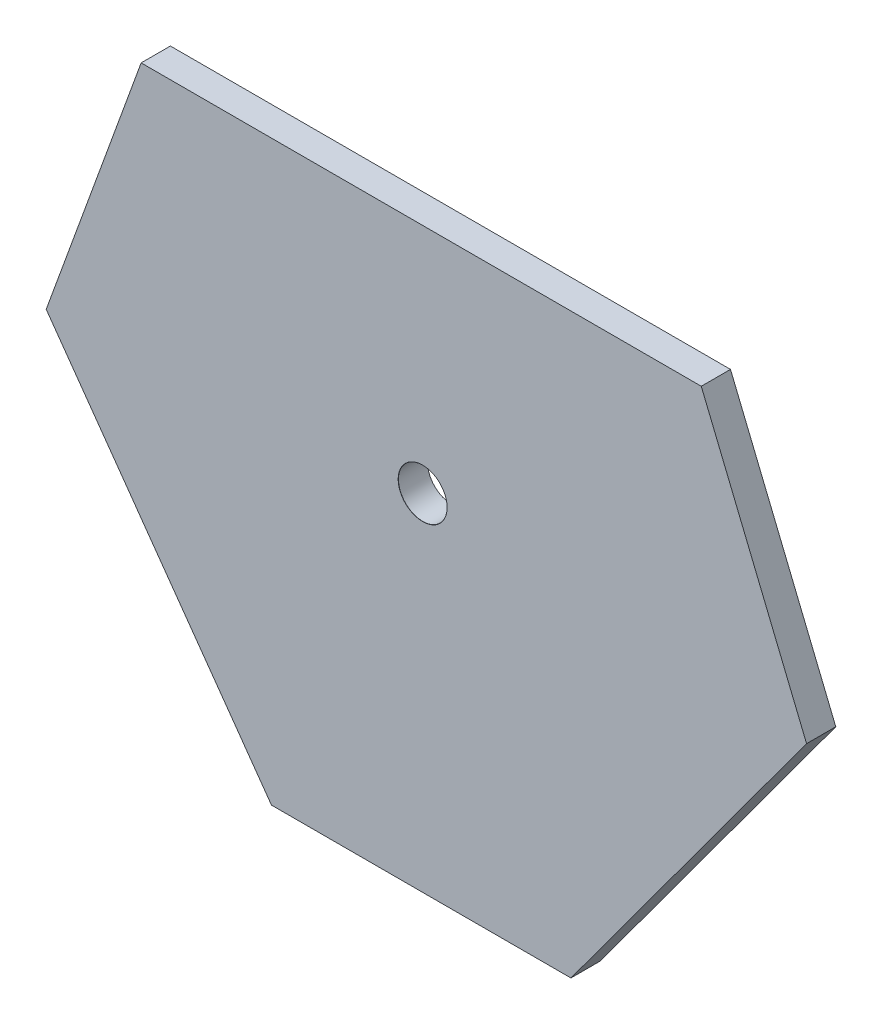
SolidWorks part; units mm, degrees
ref_plane "Front Plane" through (0, 0, 0) normal (0, 0, 1) x (1, 0, 0)
ref_plane "Top Plane" through (0, 0, 0) normal (0, 1, 0) x (1, 0, 0)
ref_plane "Right Plane" through (0, 0, 0) normal (1, 0, 0) x (0, 0, -1)
sketch "Sketch1" plane through (0, 0, 0) normal (0, 0, 1) x (1, 0, 0)
  line L0 (-47.9271, -8.0808) -> (13.5529, -8.0808) construction
  line L1 (-47.9271, -8.0808) -> (13.5529, -8.0808)
  line L3 (-74.6871, 110.5195) -> (40.3129, 110.5195)
  line L4 (-74.6871, 110.5195) -> (-94.1823, 56.957)
  line L5 (40.3129, 110.5195) -> (61.9322, 57.7786)
  line L6 (-94.1823, 56.957) -> (-47.9271, -8.0808)
  line L7 (13.5529, -8.0808) -> (61.9322, 57.7786)
  point P2 (0, 0)
  point P9 (-17.1871, 110.5195)
extrude "Boss-Extrude1" add sketch "Sketch1" along normal blind 6
hole_wizard "Ø10.0mm Dowel Hole2" positions "Sketch4" profile "Sketch5" hole size "Ø10.0" standard "GB"
sketch "Sketch4" plane through (0, 0, 6) normal (0, 0, 1) x (1, 0, 0)
  point P0 (-16.8906, 62.8731)
sketch "Sketch5" plane through (-16.8906, 62.8731, 6) normal (1, 0, 0) x (0, -1, 0)
  line L0 (0, 0) -> (0, 53.0043)
  line L1 (0, 53.0043) -> (5, 50)
  line L2 (5, 50) -> (5, 0.025)
  line L3 (5, 0.025) -> (5.025, 0)
  line L5 (5.025, 0) -> (0, 0)
  line L6 (-5, 0.025) -> (-5.025, 0) construction
  line L10 (0, 53.0043) -> (-5, 50) construction
  line L11 (0, -6.35) -> (0, 107.95) construction
  dimension "Hole Dia." = 10
  dimension "Hole Depth" = 50
  dimension "Near C'Sink Dia." = 10.05
  dimension "Near C'Sink Angle" = 90
  dimension "Drill Angle" = 118
